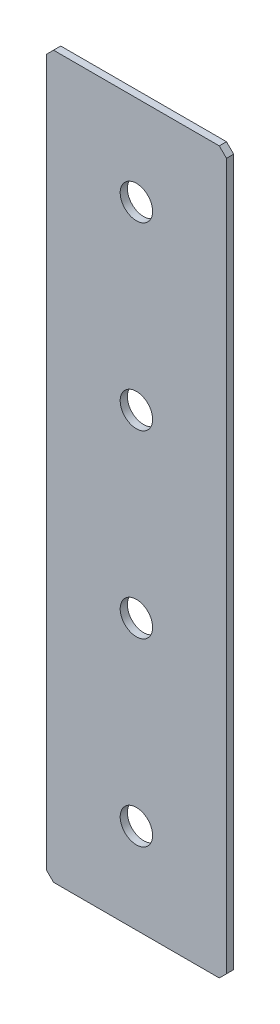
SolidWorks part; units mm, degrees
material "Простая углеродистая сталь"
ref_plane "Спереди(Плоскость XY)" through (0, 0, 0) normal (0, 0, 1) x (1, 0, 0)
ref_plane "Сверху(Плоскость XZ)" through (0, 0, 0) normal (0, 1, 0) x (1, 0, 0)
ref_plane "Справа(Плоскость ZY)" through (0, 0, 0) normal (1, 0, 0) x (0, 0, -1)
sketch "Эскиз1" plane through (0, 0, 0) normal (0, 0, 1) x (1, 0, 0)
  line L1 (-25, -100) -> (25, -100)
  line L2 (-25, -100) -> (-25, 100)
  line L3 (-25, 100) -> (25, 100)
  line L4 (25, -100) -> (25, 100)
  line L5 (-25, -100) -> (25, 100) construction
  line L6 (-25, 100) -> (25, -100) construction
  point P0 (0, 0)
  dimension "D1" = 50
  dimension "D2" = 200
extrude "Бобышка-Вытянуть1" add sketch "Эскиз1" along normal blind 2
chamfer "Фаска1" distance 2 angle 45 4 edges at (-25, -100, 1) (25, -100, 1) (-25, 100, 1) (25, 100, 1)
hole_wizard "Отверстие с зазором M81" positions "Эскиз2" profile "Эскиз3" hole size "M8" standard "DIN" end condition through all
sketch "Эскиз2" plane through (0, 0, 2) normal (0, 0, 1) x (1, 0, 0)
  line L15 (0, 25) -> (0, 75) construction
  line L17 (0, 25) -> (0, -25) construction
  line L18 (0, -25) -> (0, -75) construction
  point P204 (0, 75)
  point P206 (0, 25)
  point P208 (0, -25)
  point P210 (0, -75)
  dimension "D2" = 50
sketch "Эскиз3" plane through (0, 75, 2) normal (1, 0, 0) x (0, -1, 0)
  line L0 (0, 0) -> (0, 2)
  line L1 (0, 2) -> (4.5, 2)
  line L2 (4.5, 2) -> (4.5, 0)
  line L5 (4.5, 0) -> (0, 0)
  line L11 (0, -6.35) -> (0, 107.95) construction
  dimension "Диаметр сквозного отверстия" = 9
  dimension "Глубина сквозного отверстия" = 2
